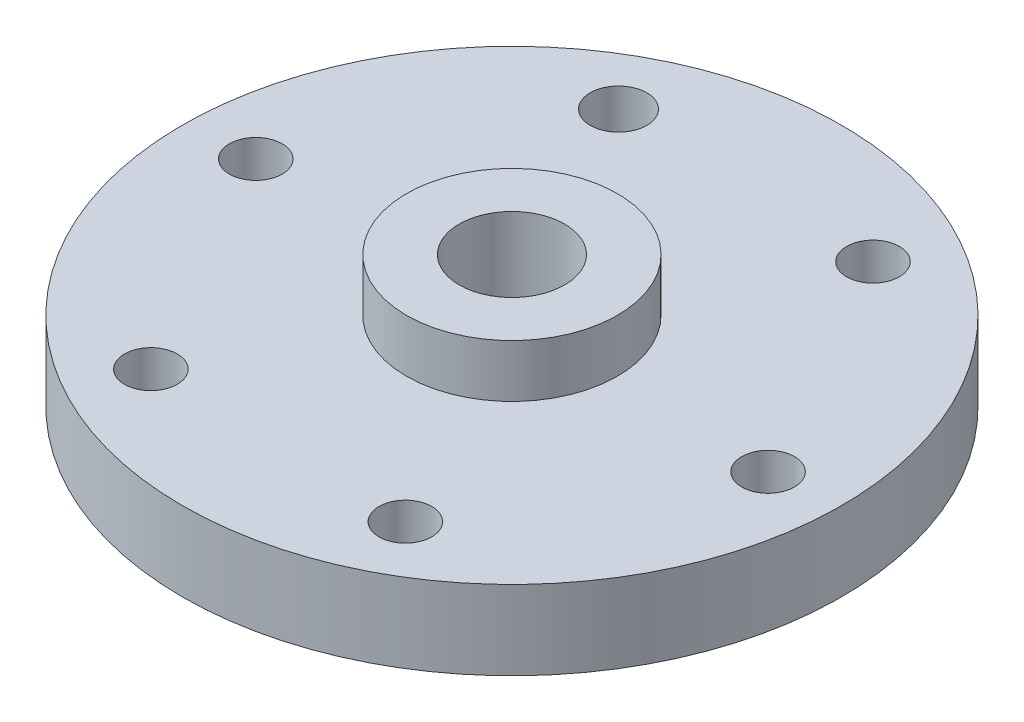
SolidWorks part; units mm, degrees
ref_plane "Front Plane" through (0, 0, 0) normal (0, 0, 1) x (1, 0, 0)
ref_plane "Top Plane" through (0, 0, 0) normal (0, 1, 0) x (1, 0, 0)
ref_plane "Right Plane" through (0, 0, 0) normal (1, 0, 0) x (0, 0, -1)
sketch "Sketch1" plane through (0, 0, 0) normal (0, 1, 0) x (1, 0, 0)
  circle A0 centre (0, 0) radius 12.5
  dimension "D1" = 25
extrude "Boss-Extrude1" add sketch "Sketch1" along normal blind 3 contours A0
sketch "Sketch2" plane through (0, 0, 0) normal (0, 1, 0) x (1, 0, 0)
  circle A0 centre (0, 0) radius 4
  circle A2 centre (0, 0) radius 12.5 construction
  dimension "D1" = 8
extrude "Boss-Extrude2" add sketch "Sketch2" along normal blind 5 contours A0
sketch "Sketch3" plane through (0, 0, 0) normal (0, 1, 0) x (1, 0, 0)
  line L1 (4.919, -8.7067) -> (9.9998, -0.0934) construction
  line L2 (9.9998, -0.0934) -> (5.0808, 8.6133) construction
  line L3 (5.0808, 8.6133) -> (-4.919, 8.7067) construction
  line L4 (-4.919, 8.7067) -> (-9.9998, 0.0934) construction
  line L5 (-9.9998, 0.0934) -> (-5.0808, -8.6133) construction
  line L6 (-5.0808, -8.6133) -> (4.919, -8.7067) construction
  circle A0 centre (0, 0) radius 8.6604 construction
  circle A1 centre (-4.919, 8.7067) radius 1
  circle A3 centre (-9.9998, 0.0934) radius 1
  circle A4 centre (-5.0808, -8.6133) radius 1
  circle A5 centre (4.919, -8.7067) radius 1.0219
  circle A6 centre (9.9998, -0.0934) radius 1
  dimension "D2" = 9.9998
  dimension "D1" = 10.0002
sketch "Sketch4" plane through (0, 3, 0) normal (0, 1, 0) x (1, 0, 0)
  circle A0 centre (9.9998, -0.0934) radius 1
  circle A1 centre (5.0808, 8.6133) radius 1
  dimension "D1" = 2
sketch "Sketch5" plane through (0, 5, 0) normal (0, 1, 0) x (1, 0, 0)
  circle A0 centre (0, 0) radius 2
  dimension "D1" = 4
extrude "Cut-Extrude3" cut sketch "Sketch5" against normal blind 8 contours A0
extrude "Cut-Extrude4" cut sketch "Sketch4" against normal blind 8 contours A1
extrude "Cut-Extrude7" cut sketch "Sketch3" along normal blind 3 contours A4
sketch "Sketch11" plane through (0, 3, 0) normal (0, 1, 0) x (1, 0, 0)
  line L1 (-9.9961, 0.2808) -> (-5.2412, -8.5165) construction
  line L2 (-5.2412, -8.5165) -> (4.7549, -8.7972) construction
  line L3 (4.7549, -8.7972) -> (9.9961, -0.2808) construction
  line L4 (9.9961, -0.2808) -> (5.2412, 8.5165) construction
  line L5 (5.2412, 8.5165) -> (-4.7549, 8.7972) construction
  line L6 (-4.7549, 8.7972) -> (-9.9961, 0.2808) construction
  circle A0 centre (0, 0) radius 10 construction
  circle A1 centre (-4.7549, 8.7972) radius 1.0731
  circle A2 centre (-9.9961, 0.2808) radius 1
  circle A3 centre (4.7549, -8.7972) radius 1
  circle A4 centre (9.9961, -0.2808) radius 1
extrude "Cut-Extrude9" cut sketch "Sketch11" against normal blind 3 contours A3 | A4 | A1 | A2
